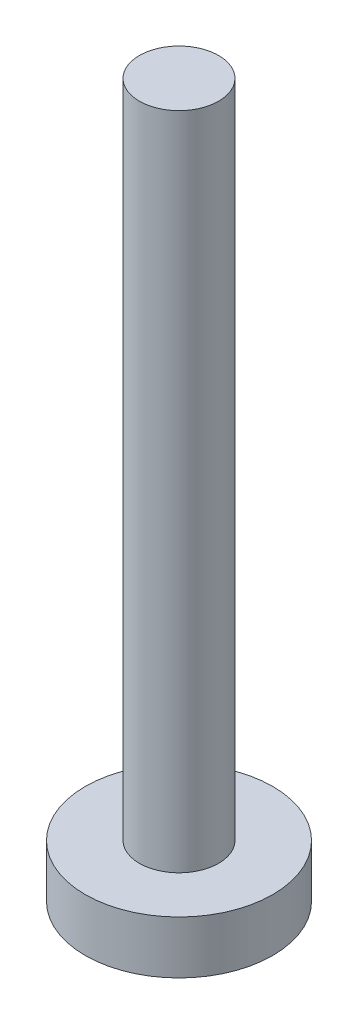
SolidWorks part; units mm, degrees
ref_plane "前视基准面" through (0, 0, 0) normal (0, 0, 1) x (1, 0, 0)
ref_plane "上视基准面" through (0, 0, 0) normal (0, 1, 0) x (1, 0, 0)
ref_plane "右视基准面" through (0, 0, 0) normal (1, 0, 0) x (0, 0, -1)
sketch "草图1" plane through (0, 0, 0) normal (0, 1, 0) x (1, 0, 0)
  circle A0 centre (0, 0) radius 3.55
  dimension "D1" = 7.1
extrude "凸台-拉伸1" add sketch "草图1" along normal blind 2
sketch "草图2" plane through (0, 2, 0) normal (0, 1, 0) x (1, 0, 0)
  circle A0 centre (0, 0) radius 1.5
  dimension "D1" = 3
extrude "凸台-拉伸2" add sketch "草图2" along normal blind 25
